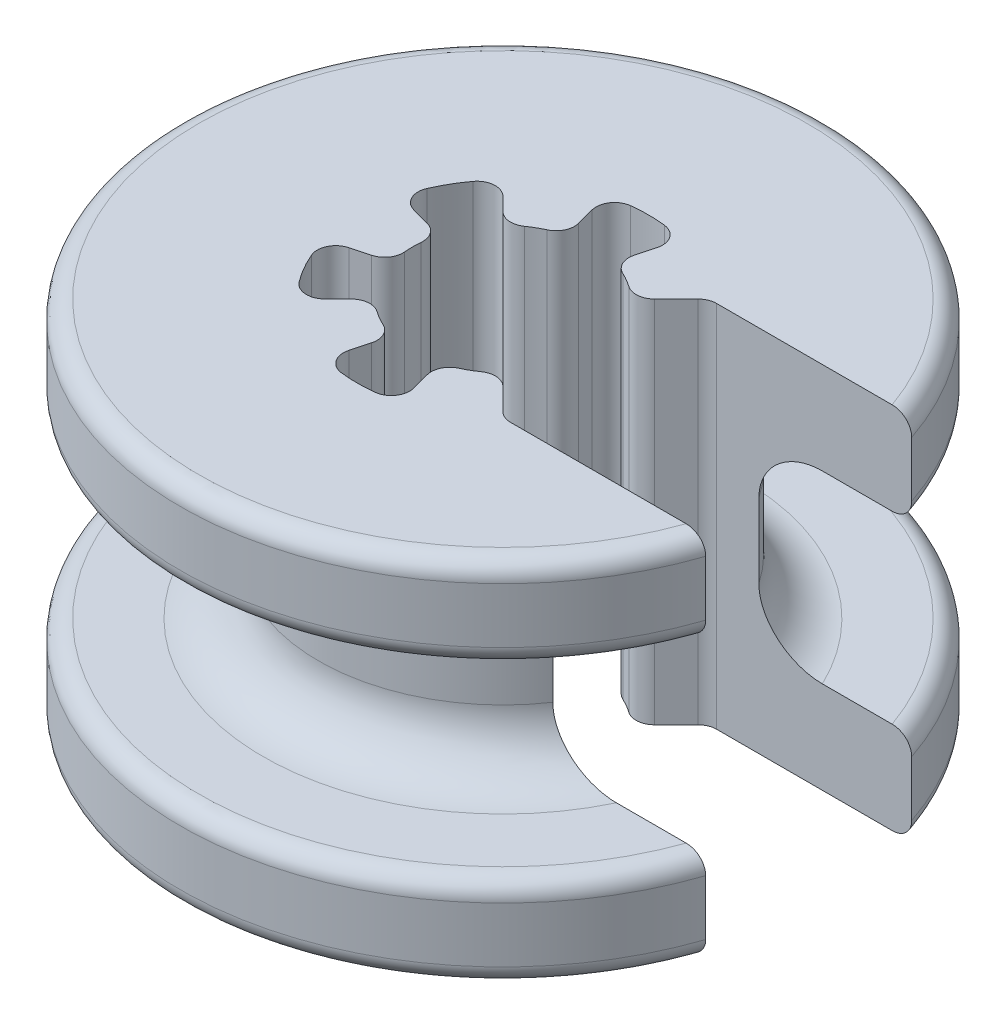
SolidWorks part; units mm, degrees
ref_plane "Front Plane" through (0, 0, 0) normal (0, 0, 1) x (1, 0, 0)
ref_plane "Top Plane" through (0, 0, 0) normal (0, 1, 0) x (1, 0, 0)
ref_plane "Right Plane" through (0, 0, 0) normal (1, 0, 0) x (0, 0, -1)
sketch "Sketch1" plane through (0, 0, 0) normal (0, 1, 0) x (1, 0, 0)
  line L0 (2.7931, 2.7931) -> (8.2922, 2.7931)
  line L1 (0.6341, 2.3665) -> (1.0223, 3.8154)
  line L2 (2.7931, -2.7931) -> (8.2922, -2.7931)
  line L3 (1.7324, 1.7324) -> (2.7931, 2.7931)
  line L9 (1.7324, -1.7324) -> (2.7931, -2.7931)
  line L11 (0.6341, -2.3665) -> (1.0223, -3.8154)
  line L13 (-0.6341, -2.3665) -> (-1.0223, -3.8154)
  line L15 (-1.7324, -1.7324) -> (-2.7931, -2.7931)
  line L17 (-2.3665, -0.6341) -> (-3.8154, -1.0223)
  line L19 (-2.3665, 0.6341) -> (-3.8154, 1.0223)
  line L21 (-1.7324, 1.7324) -> (-2.7931, 2.7931)
  line L23 (-0.6341, 2.3665) -> (-1.0223, 3.8154)
  arc A0 (1.0223, 3.8154) -> (-1.0223, 3.8154) centre (0, 0) ccw
  arc A2 (8.2922, 2.7931) -> (8.2922, -2.7931) centre (0, 0) ccw
  arc A3 (1.7324, 1.7324) -> (0.6341, 2.3665) centre (0, 0) ccw
  arc A4 (-0.6341, 2.3665) -> (-1.7324, 1.7324) centre (0, 0) ccw
  arc A5 (-2.3665, 0.6341) -> (-2.3665, -0.6341) centre (0, 0) ccw
  arc A6 (-1.7324, -1.7324) -> (-0.6341, -2.3665) centre (0, 0) ccw
  arc A7 (0.6341, -2.3665) -> (1.7324, -1.7324) centre (0, 0) ccw
  arc A8 (-2.7931, 2.7931) -> (-3.8154, 1.0223) centre (0, 0) ccw
  arc A9 (-3.8154, -1.0223) -> (-2.7931, -2.7931) centre (0, 0) ccw
  arc A10 (-1.0223, -3.8154) -> (1.0223, -3.8154) centre (0, 0) ccw
extrude "Boss-Extrude1" add sketch "Sketch1" along normal blind 2.5
sketch "Sketch3" plane through (0, 2.5, 0) normal (0, 1, 0) x (1, 0, 0)
  line L0 (2.7931, 2.7931) -> (4.1471, 2.7931)
  line L1 (2.7931, 2.7931) -> (8.2922, 2.7931) construction
  line L2 (2.7931, -2.7931) -> (4.1471, -2.7931)
  line L3 (2.7931, 2.7931) -> (1.7324, 1.7324)
  line L4 (1.7324, 1.7324) -> (2.7931, 2.7931) construction
  line L5 (1.0223, 3.8154) -> (0.6341, 2.3665)
  line L6 (-1.0223, 3.8154) -> (-0.6341, 2.3665)
  line L7 (-2.7931, 2.7931) -> (-1.7324, 1.7324)
  line L8 (-3.8154, 1.0223) -> (-2.3665, 0.6341)
  line L9 (-3.8154, -1.0223) -> (-2.3665, -0.6341)
  line L10 (-2.7931, -2.7931) -> (-1.7324, -1.7324)
  line L11 (-0.6341, -2.3665) -> (-1.0223, -3.8154)
  line L12 (0.6341, -2.3665) -> (1.0223, -3.8154)
  line L13 (1.7324, -1.7324) -> (2.7931, -2.7931)
  arc A1 (1.7324, 1.7324) -> (0.6341, 2.3665) centre (0, 0) ccw
  arc A2 (4.1471, 2.7931) -> (4.1471, -2.7931) centre (0, 0) ccw
  arc A3 (-0.6341, 2.3665) -> (-1.7324, 1.7324) centre (0, 0) ccw
  arc A4 (-2.3665, 0.6341) -> (-2.3665, -0.6341) centre (0, 0) ccw
  arc A5 (-1.7324, -1.7324) -> (-0.6341, -2.3665) centre (0, 0) ccw
  arc A6 (0.6341, -2.3665) -> (1.7324, -1.7324) centre (0, 0) ccw
  arc A7 (1.0223, 3.8154) -> (-1.0223, 3.8154) centre (0, 0) ccw
  arc A9 (-2.7931, 2.7931) -> (-3.8154, 1.0223) centre (0, 0) ccw
  arc A10 (-3.8154, -1.0223) -> (-2.7931, -2.7931) centre (0, 0) ccw
  arc A11 (-1.0223, -3.8154) -> (1.0223, -3.8154) centre (0, 0) ccw
  dimension "D2" = 10
extrude "Boss-Extrude2" add sketch "Sketch3" along normal blind 5
sketch "Sketch4" plane through (0, 7.5, 0) normal (0, 1, 0) x (1, 0, 0)
  line L0 (1.7324, 1.7324) -> (2.7931, 2.7931)
  line L1 (8.2922, -2.7931) -> (2.7931, -2.7931)
  line L2 (2.7931, -2.7931) -> (1.7324, -1.7324)
  line L3 (2.7931, 2.7931) -> (8.2922, 2.7931)
  line L4 (1.0223, 3.8154) -> (0.6341, 2.3665)
  line L5 (-1.0223, 3.8154) -> (-0.6341, 2.3665)
  line L6 (-2.7931, 2.7931) -> (-1.7324, 1.7324)
  line L7 (-3.8154, 1.0223) -> (-2.3665, 0.6341)
  line L8 (-3.8154, -1.0223) -> (-2.3665, -0.6341)
  line L9 (-1.7324, -1.7324) -> (-2.7931, -2.7931)
  line L10 (-0.6341, -2.3665) -> (-1.0223, -3.8154)
  line L11 (-1.0223, -3.8154) -> (-0.6341, -2.3665) construction
  line L12 (0.6341, -2.3665) -> (1.0223, -3.8154)
  arc A1 (1.0223, 3.8154) -> (-1.0223, 3.8154) centre (0, 0) ccw
  arc A2 (-0.6341, 2.3665) -> (-1.7324, 1.7324) centre (0, 0) ccw
  arc A3 (8.2922, 2.7931) -> (8.2922, -2.7931) centre (0, 0) ccw
  arc A4 (-2.3665, 0.6341) -> (-2.3665, -0.6341) centre (0, 0) ccw
  arc A5 (-1.7324, -1.7324) -> (-0.6341, -2.3665) centre (0, 0) ccw
  arc A6 (0.6341, -2.3665) -> (1.7324, -1.7324) centre (0, 0) ccw
  arc A7 (1.7324, 1.7324) -> (0.6341, 2.3665) centre (0, 0) ccw
  arc A8 (-2.7931, 2.7931) -> (-3.8154, 1.0223) centre (0, 0) ccw
  arc A9 (-3.8154, -1.0223) -> (-2.7931, -2.7931) centre (0, 0) ccw
  arc A10 (-1.0223, -3.8154) -> (1.0223, -3.8154) centre (0, 0) ccw
extrude "Boss-Extrude3" add sketch "Sketch4" along normal blind 2.5
fillet "Fillet1" radius 0.5 20 edges at (2.7931, 5, -2.7931) (2.7931, 5, 2.7931) (1.7324, 5, 1.7324) (0.6341, 5, 2.3665) (1.0223, 5, 3.8154) (-1.0223, 5, 3.8154) (-0.6341, 5, 2.3665) (-1.7324, 5, 1.7324) (-2.7931, 5, 2.7931) (-3.8154, 5, 1.0223) (-2.3665, 5, 0.6341) (-2.3665, 5, -0.6341) (-3.8154, 5, -1.0223) (-2.7931, 5, -2.7931) (-1.7324, 5, -1.7324) (-0.6341, 5, -2.3665) (-1.0223, 5, -3.8154) (1.0223, 5, -3.8154) (0.6341, 5, -2.3665) (1.7324, 5, -1.7324)
fillet "Fillet2" radius 1.5 2 edges at (-5, 2.5, 0) (-5, 7.5, 0)
fillet "Fillet3" radius 0.5 4 edges at (-8.75, 0, 0) (-8.75, 2.5, 0) (-8.75, 10, 0) (-8.75, 7.5, 0)
